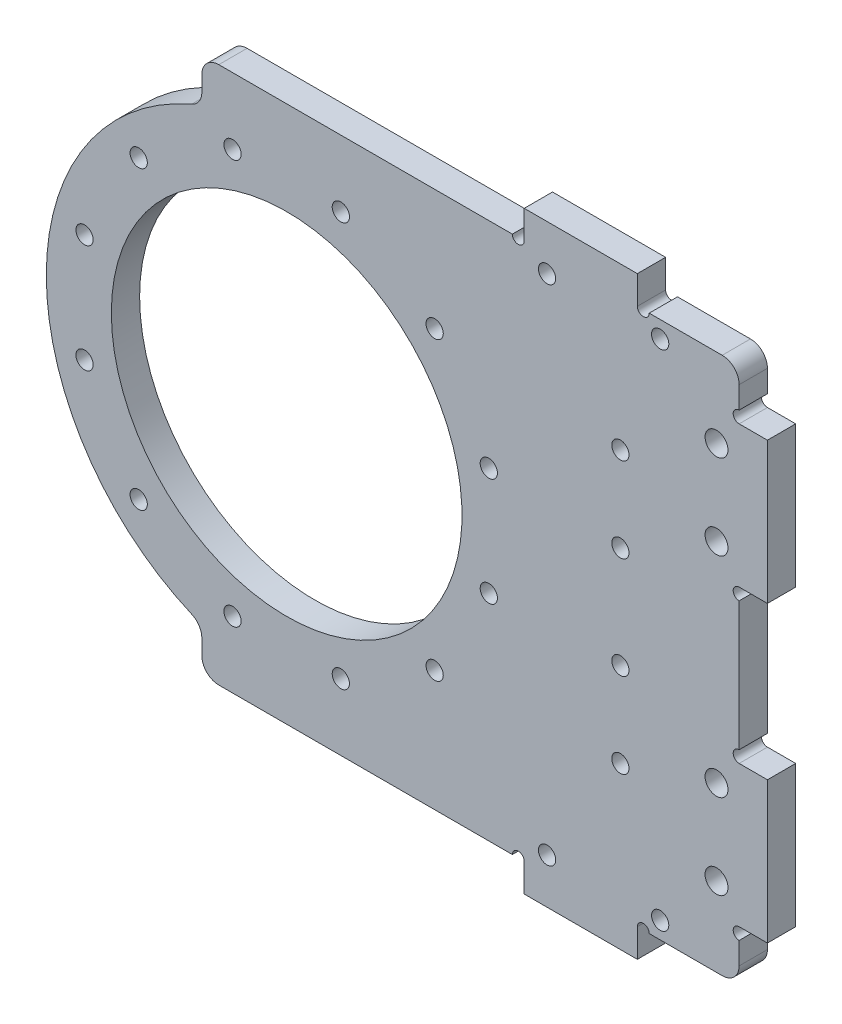
SolidWorks part; units mm, degrees
material "Thornel Mat VMA"
ref_plane "前视基准面" through (0, 0, 0) normal (0, 0, 1) x (1, 0, 0)
ref_plane "上视基准面" through (0, 0, 0) normal (0, 1, 0) x (1, 0, 0)
ref_plane "右视基准面" through (0, 0, 0) normal (1, 0, 0) x (0, 0, -1)
other "Configuration Table"
sketch "草图1" plane through (0, 0, 0) normal (0, 0, 1) x (1, 0, 0)
  line L0 (80, 47.5) -> (80, -47.5)
  line L1 (80, 47.5) -> (15, 47.5)
  line L2 (15, 47.5) -> (-10.2186, 41.2532)
  line L3 (-10.2186, -41.2532) -> (15, -47.5)
  line L4 (15, -47.5) -> (80, -47.5)
  arc A0 (-10.2186, 41.2532) -> (-10.2186, -41.2532) centre (0, 0) ccw
  point P5 (80, 0)
  dimension "D1" = 85
  dimension "D2" = 95
  dimension "D3" = 80
  dimension "D4" = 65
extrude "凸台-拉伸1" add sketch "草图1" along normal mid plane 5
fillet "圆角2" radius 10 2 edges at (15, 47.5, 0) (15, -47.5, 0)
fillet "圆角3" radius 3 2 edges at (80, -47.5, 0) (80, 47.5, 0)
sketch "草图2" plane through (0, 0, -2.5) normal (0, 0, -1) x (-1, 0, 0)
  circle A0 centre (0, 0) radius 31
  dimension "D1" = 62
extrude "切除-拉伸1" cut sketch "草图2" against normal through all both and the other way through all
sketch "草图3" plane through (0, 0, 2.5) normal (0, 0, 1) x (1, 0, 0)
  line L1 (0, 0) -> (0, 37) construction
  line L2 (0, 0) -> (9.5763, 35.7393) construction
  circle A0 centre (0, 0) radius 37 construction
  circle A1 centre (9.5763, 35.7393) radius 1.525
  circle A2 centre (26.163, 26.163) radius 1.525
  circle A3 centre (35.7393, 9.5763) radius 1.525
  circle A4 centre (35.7393, -9.5763) radius 1.525
  circle A5 centre (26.163, -26.163) radius 1.525
  circle A6 centre (9.5763, -35.7393) radius 1.525
  circle A7 centre (-9.5763, -35.7393) radius 1.525
  circle A8 centre (-26.163, -26.163) radius 1.525
  circle A9 centre (-35.7393, -9.5763) radius 1.525
  circle A10 centre (-35.7393, 9.5763) radius 1.525
  circle A11 centre (-26.163, 26.163) radius 1.525
  circle A12 centre (-9.5763, 35.7393) radius 1.525
  point P31 (0, 0)
  dimension "D1" = 74
  dimension "D3" = 3.05
  dimension "D2" = 15
  dimension "D4" = 12
extrude "切除-拉伸2" cut sketch "草图3" against normal through all both
sketch "草图4" plane through (0, 0, 2.5) normal (0, 0, 1) x (1, 0, 0)
  line L0 (80, -44.5) -> (80, 44.5) construction
  line L1 (77, 47.5) -> (16.2201, 47.5) construction
  circle A0 centre (76, -33.5) radius 2.025
  circle A1 centre (76, -18.5) radius 2.025
  circle A2 centre (76, 18.5) radius 2.025
  circle A3 centre (76, 33.5) radius 2.025
  circle A8 centre (76, -33.5) radius 2.025 construction
  dimension "D1" = 4.05
  dimension "D2" = 4
  dimension "D3" = 15
  dimension "D4" = 15
  dimension "D5" = 29
  dimension "D6" = 4
extrude "切除-拉伸3" cut sketch "草图4" against normal through all
sketch "草图6" plane through (0, 0, 2.5) normal (0, 0, 1) x (1, 0, 0)
  line L0 (-15, 39.7649) -> (-15, 44.5)
  line L1 (-12, 47.5) -> (77, 47.5)
  line L2 (77, 47.5) -> (16.2201, 47.5) construction
  line L3 (-15, 39.7649) -> (16.2201, 47.5)
  line L4 (80, -44.5) -> (80, 44.5) construction
  arc A1 (-15, 44.5) -> (-12, 47.5) centre (-12, 44.5) cw
  arc A2 (-10.2186, 41.2532) -> (-10.2186, -41.2532) centre (0, 0) ccw construction
  arc M8 (16.2201, 47.5) -> (13.8157, 47.2066) centre (16.2201, 37.5) ccw
  line M9 (13.8157, 47.2066) -> (-10.2186, 41.2532)
  dimension "D1" = 3
  dimension "D2" = 95
extrude "凸台-拉伸2" add sketch "草图6" against normal up to surface (5 mm away) contours A1 L0 L1 M9 M8 up to face at (78.025, -33.5, -2.5)
mirror "镜向1" about plane through (0, 0, 0) normal (0, 1, 0) of "凸台-拉伸2"
fillet "圆角4" radius 3 2 edges at (-15, -39.7649, 0) (-15, 39.7649, 0)
sketch "草图8" plane through (0, 0, 2.5) normal (0, 0, 1) x (1, 0, 0)
  circle A0 centre (66.0374, 44.5) radius 1.525
  circle A1 centre (46.0374, 44.5) radius 1.525
  circle A2 centre (46.0374, 44.5) radius 1.25 construction
  circle A3 centre (66.0374, 44.5) radius 1.25 construction
  dimension "D1" = 3.05
extrude "切除-拉伸6" cut sketch "草图8" against normal blind 10
sketch "草图9" plane through (0, 47.5, 0) normal (0, 1, 0) x (1, 0, 0)
  line L0 (77, -2.5) -> (-12, -2.5) construction
  line L1 (62, 2.5) -> (42, 2.5)
  line L2 (62, 2.5) -> (62, -2.5)
  line L3 (62, -2.5) -> (42, -2.5)
  line L4 (42, 2.5) -> (42, -2.5)
  line L5 (62, 2.5) -> (42, -2.5) construction
  line L6 (62, -2.5) -> (42, 2.5) construction
  line L7 (77, 2.5) -> (-12, 2.5) construction
  line L8 (80, 2.5) -> (80, -2.5) construction
  point P0 (52, 0)
  dimension "D1" = 20
  dimension "D2" = 18
extrude "凸台-拉伸3" add sketch "草图9" along normal blind 5
sketch "草图10" plane through (0, 0, 2.5) normal (0, 0, 1) x (1, 0, 0)
  line L0 (77, 47.5) -> (62, 47.5) construction
  line L1 (42, 47.5) -> (-12, 47.5) construction
  line L2 (39.9, 47.5) -> (42, 47.5)
  line L3 (62, 47.5) -> (64.1, 47.5)
  arc A0 (62, 47.5) -> (64.1, 47.5) centre (63.05, 47.5) ccw
  arc A1 (42, 47.5) -> (39.9, 47.5) centre (40.95, 47.5) cw
  dimension "D2" = 1.05
  dimension "D1" = 1.05
extrude "切除-拉伸7" cut sketch "草图10" against normal blind 14
mirror "镜向3" about plane through (0, 0, 0) normal (0, 1, 0) of "切除-拉伸6", "凸台-拉伸3"
sketch "草图11" plane through (80, 0, 0) normal (1, 0, 0) x (0, 0, -1)
  line L6 (-2.5, 35.525) -> (-2.5, 31.475) construction
  line L7 (-2.5, 20.525) -> (-2.5, 16.475) construction
  line L8 (-2.5, 35.525) -> (-2.5, 31.475) construction
  line L9 (-2.5, 20.525) -> (-2.5, 16.475) construction
  line L10 (-2.5, 20.525) -> (-2.5, 31.475) construction
  line L11 (-2.5, 26) -> (2.5, 26) construction
  line L12 (2.5, -44.5) -> (2.5, 44.5) construction
  line L13 (-2.5, -44.5) -> (-2.5, 44.5) construction
  line L14 (-2.5, 13.5) -> (2.5, 13.5)
  line L15 (-2.5, 13.5) -> (-2.5, 38.5)
  line L16 (-2.5, 38.5) -> (2.5, 38.5)
  line L17 (2.5, 13.5) -> (2.5, 38.5)
  point P14 (-2.5, 26)
  dimension "D1" = 25
extrude "凸台-拉伸4" add sketch "草图11" along normal blind 5
sketch "草图12" plane through (0, 0, 2.5) normal (0, 0, 1) x (1, 0, 0)
  line L0 (80, 38.5) -> (80, 44.5) construction
  line L1 (80, -44.5) -> (80, 13.5) construction
  line L2 (80, 11.4) -> (80, 13.5)
  line L3 (80, 40.6) -> (80, 38.5)
  arc A0 (80, 38.5) -> (80, 40.6) centre (80, 39.55) cw
  arc A1 (80, 13.5) -> (80, 11.4) centre (80, 12.45) ccw
  dimension "D1" = 1.05
extrude "切除-拉伸8" cut sketch "草图12" against normal blind 5
mirror "镜向4" about plane through (0, 0, 0) normal (0, 1, 0) of "凸台-拉伸4", "切除-拉伸8"
sketch "草图13" plane through (0, 0, 2.5) normal (0, 0, 1) x (1, 0, 0)
  line L0 (0, 0) -> (50000, 0) construction
  line L1 (59, 24) -> (59, 9) construction
  line L2 (80, -11.4) -> (80, 11.4) construction
  circle A0 centre (59, 9) radius 1.525
  circle A1 centre (59, 24) radius 1.525
  dimension "D2" = 3.05
  dimension "D3" = 21
  dimension "D4" = 15
  dimension "D1" = 9
extrude "切除-拉伸9" cut sketch "草图13" against normal through all
mirror "镜向5" about plane through (0, 0, 0) normal (0, 1, 0) of "切除-拉伸9"
mirror "镜向6" about plane through (0, 0, 0) normal (0, 1, 0) of "切除-拉伸7", "凸台-拉伸3"
